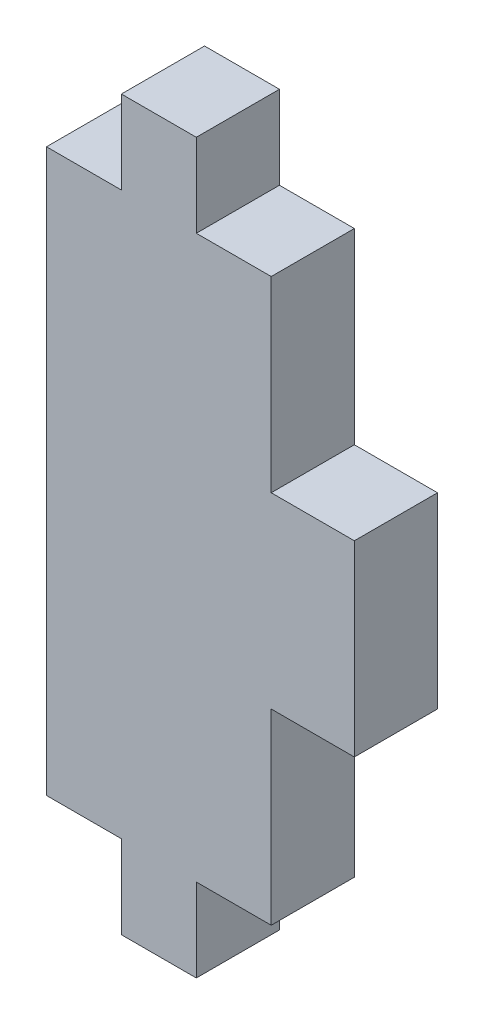
SolidWorks part; units mm, degrees
ref_plane "Front Plane" through (0, 0, 0) normal (0, 0, 1) x (1, 0, 0)
ref_plane "Top Plane" through (0, 0, 0) normal (0, 1, 0) x (1, 0, 0)
ref_plane "Right Plane" through (0, 0, 0) normal (1, 0, 0) x (0, 0, -1)
sketch "Sketch1" plane through (0, 0, 0) normal (0, 0, 1) x (1, 0, 0)
  line L0 (8.4667, 31.75) -> (12.7, 31.75)
  line L1 (0, 0) -> (4.2333, 0)
  line L2 (0, 0) -> (0, 31.75)
  line L3 (0, 31.75) -> (4.2333, 31.75)
  line L4 (12.7, 0) -> (12.7, 10.5833)
  line L5 (12.7, 21.1667) -> (12.7, 31.75)
  line L6 (4.2333, 31.75) -> (4.2333, 36.449)
  line L7 (4.2333, 36.449) -> (8.4667, 36.449)
  line L8 (8.4667, 31.75) -> (8.4667, 36.449)
  line L9 (12.7, 21.1667) -> (17.399, 21.1667)
  line L10 (8.4667, 0) -> (12.7, 0)
  line L11 (12.7, 10.5833) -> (17.399, 10.5833)
  line L12 (17.399, 21.1667) -> (17.399, 10.5833)
  line L14 (4.2333, 0) -> (4.2333, -4.699)
  line L15 (4.2333, -4.699) -> (8.4667, -4.699)
  line L16 (8.4667, 0) -> (8.4667, -4.699)
  dimension "D1" = 4.699
  dimension "D2" = 12.7
  dimension "D3" = 31.75
extrude "Boss-Extrude1" add sketch "Sketch1" along normal blind 4.699
equation "\"mat\"= \"mat@jaws.assembly\""
equation "\"D1@Sketch1\"= \"mat\""
equation "\"D1@Boss-Extrude1\"= \"mat\""
